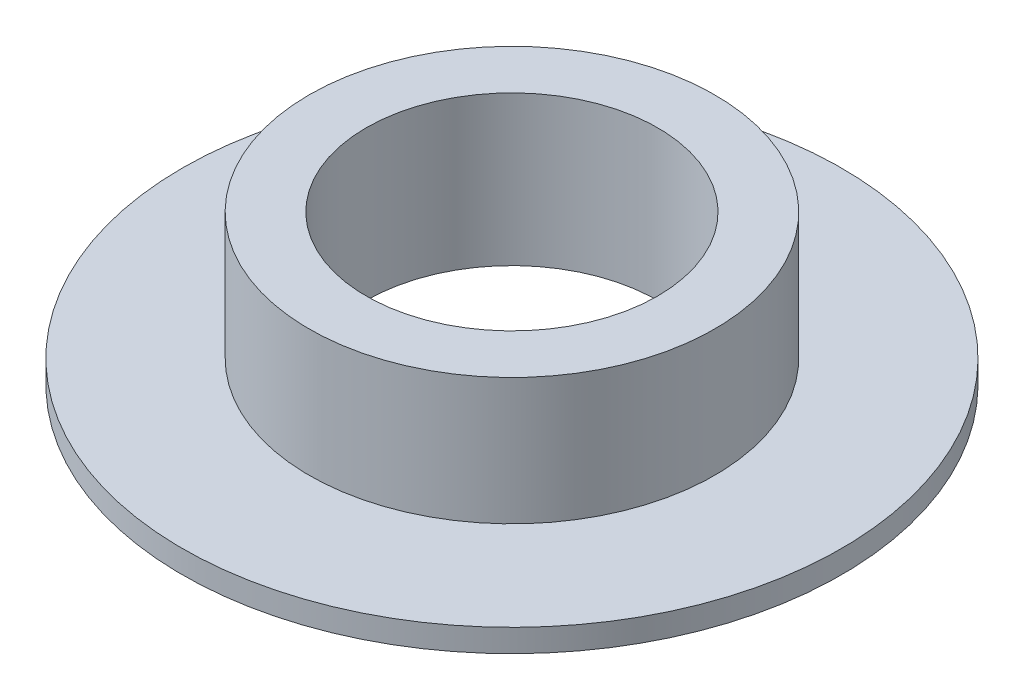
SolidWorks part; units mm, degrees
ref_plane "Alzado" through (0, 0, 0) normal (0, 0, 1) x (1, 0, 0)
ref_plane "Planta" through (0, 0, 0) normal (0, 1, 0) x (1, 0, 0)
ref_plane "Vista lateral" through (0, 0, 0) normal (1, 0, 0) x (0, 0, -1)
sketch "Croquis1" plane through (0, 0, 0) normal (0, 0, 1) x (1, 0, 0)
  line L0 (-40.0216, 13.9729) -> (-40.0216, -36.0271) construction
  line L1 (-40.0216, -11.0271) -> (-51.5216, -11.0271) construction
  line L2 (-51.5216, 8.9729) -> (-51.5216, -2.8271)
  line L3 (-40.0216, 8.9729) -> (-56.0216, 8.9729) construction
  line L4 (-51.5216, 8.9729) -> (-56.0216, 8.9729)
  line L5 (-56.0216, 8.9729) -> (-56.0216, -1.0271)
  line L6 (-56.0216, -1.0271) -> (-66.0216, -1.0271)
  line L7 (-66.0216, -1.0271) -> (-66.0216, -2.8271)
  line L8 (-66.0216, -2.8271) -> (-51.5216, -2.8271)
  dimension "D1" = 16
  dimension "D2" = 11.5
  dimension "D3" = 1.8
  dimension "D4" = 10
  dimension "D5" = 11.5
revolve "Revolución1" add sketch "Croquis1" angle 360 about L0
